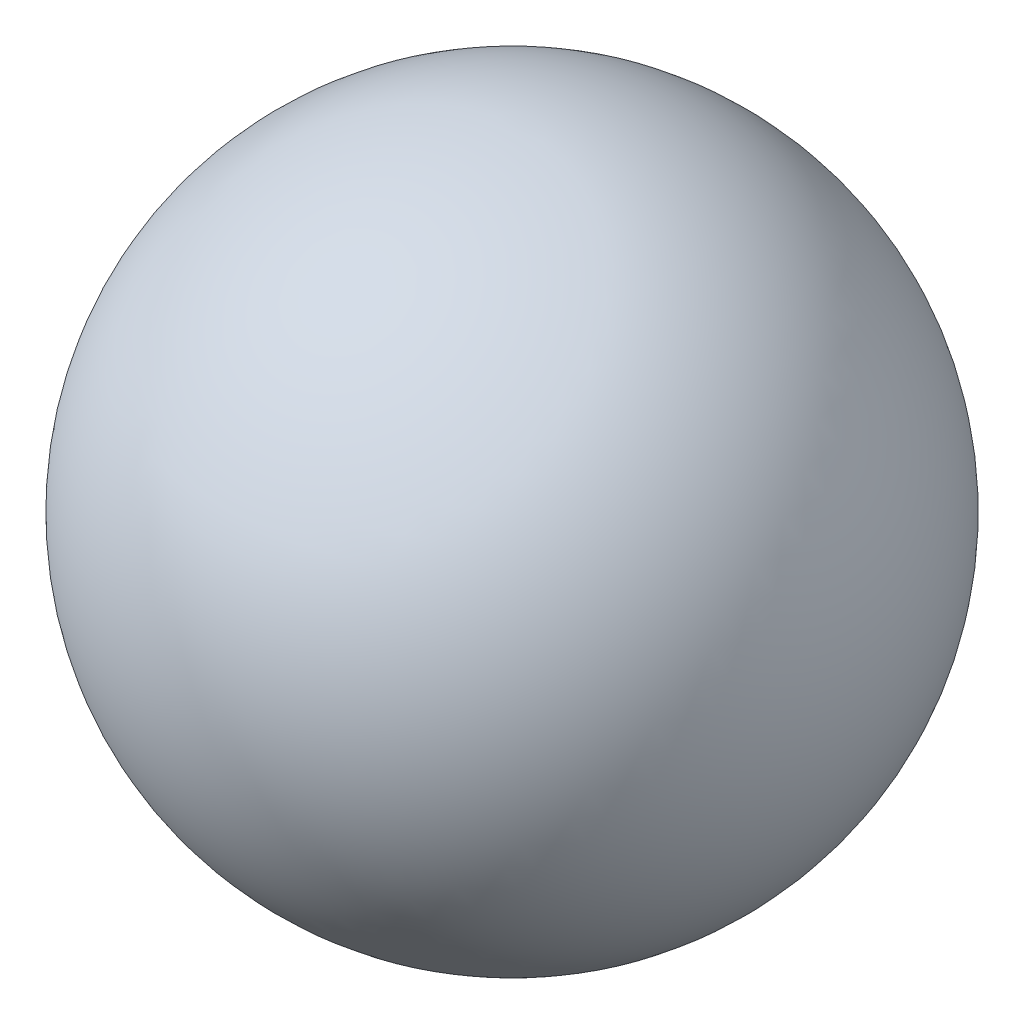
SolidWorks part; units mm, degrees
material "Chrome Stainless Steel"
ref_plane "Front Plane" through (0, 0, 0) normal (0, 0, 1) x (1, 0, 0)
ref_plane "Top Plane" through (0, 0, 0) normal (0, 1, 0) x (1, 0, 0)
ref_plane "Right Plane" through (0, 0, 0) normal (1, 0, 0) x (0, 0, -1)
sketch "Sketch1" plane through (0, 0, 0) normal (0, 0, 1) x (1, 0, 0)
  line L0 (0, 9.5) -> (0, -9.5)
  arc A0 (0, -9.5) -> (0, 9.5) centre (0, 0) ccw
  dimension "D1" = 19
revolve "Revolve1" add sketch "Sketch1" angle 360 about L0
